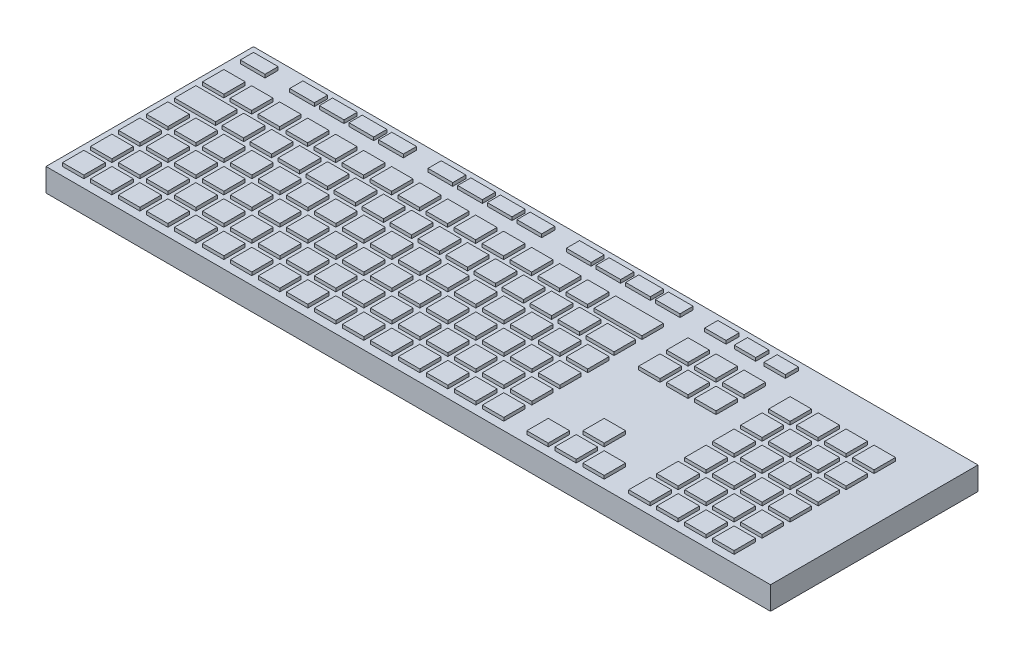
SolidWorks part; units mm, degrees
ref_plane "Front Plane" through (0, 0, 0) normal (0, 0, 1) x (1, 0, 0)
ref_plane "Top Plane" through (0, 0, 0) normal (0, 1, 0) x (1, 0, 0)
ref_plane "Right Plane" through (0, 0, 0) normal (1, 0, 0) x (0, 0, -1)
sketch "Sketch1" plane through (0, 0, 0) normal (0, 1, 0) x (1, 0, 0)
  line L1 (-220, -63) -> (220, -63)
  line L2 (-220, -63) -> (-220, 63)
  line L3 (-220, 63) -> (220, 63)
  line L4 (220, -63) -> (220, 63)
  line L5 (-220, -63) -> (220, 63) construction
  line L6 (-220, 63) -> (220, -63) construction
  point P0 (0, 0)
  dimension "D1" = 440
  dimension "D2" = 126
extrude "Boss-Extrude1" add sketch "Sketch1" along normal blind 14
sketch "Sketch4" plane through (0, 14, 0) normal (0, 1, 0) x (1, 0, 0)
  line L0 (220, 63) -> (-220, 63) construction
  line L1 (-215, 58) -> (-200, 58)
  line L2 (-215, 58) -> (-215, 50)
  line L3 (-215, 50) -> (-200, 50)
  line L4 (-200, 58) -> (-200, 50)
  line L5 (-220, 63) -> (-220, -63) construction
  dimension "D1" = 5
  dimension "D2" = 5
  dimension "D3" = 15
  dimension "D4" = 8
extrude "Boss-Extrude2" add sketch "Sketch4" along normal blind 2
sketch "Sketch5" plane through (0, 14, 0) normal (0, 1, 0) x (1, 0, 0)
  line L0 (-200, 50) -> (-200, 58) construction
  line L1 (-185, 58) -> (-170, 58)
  line L2 (-185, 58) -> (-185, 50)
  line L3 (-185, 50) -> (-170, 50)
  line L4 (-170, 58) -> (-170, 50)
  line L5 (220, 63) -> (-220, 63) construction
  point P6 (-200, 54)
  dimension "D1" = 15
  dimension "D2" = 5
  dimension "D3" = 8
  dimension "D4" = 15
extrude "Boss-Extrude3" add sketch "Sketch5" along normal blind 2
pattern_linear "LPattern1" count 4 spacing 18 along (1, 0, 0) of "Boss-Extrude3"
sketch "Sketch6" plane through (0, 14, 0) normal (0, 1, 0) x (1, 0, 0)
  line L0 (-116, 50) -> (-116, 58) construction
  line L1 (-101, 58) -> (-86, 58)
  line L2 (-101, 58) -> (-101, 50)
  line L3 (-101, 50) -> (-86, 50)
  line L4 (-86, 58) -> (-86, 50)
  line L5 (220, 63) -> (-220, 63) construction
  dimension "D1" = 15
  dimension "D2" = 5
  dimension "D3" = 8
  dimension "D4" = 15
extrude "Boss-Extrude4" add sketch "Sketch6" along normal blind 2
pattern_linear "LPattern2" count 4 spacing 18 along (1, 0, 0) of "Boss-Extrude4"
sketch "Sketch7" plane through (0, 14, 0) normal (0, 1, 0) x (1, 0, 0)
  line L0 (220, 63) -> (-220, 63) construction
  line L1 (-17, 58) -> (-2, 58)
  line L2 (-17, 58) -> (-17, 50)
  line L3 (-17, 50) -> (-2, 50)
  line L4 (-2, 58) -> (-2, 50)
  line L5 (-32, 50) -> (-32, 58) construction
  dimension "D1" = 5
  dimension "D2" = 15
  dimension "D3" = 8
  dimension "D4" = 15
extrude "Boss-Extrude5" add sketch "Sketch7" along normal blind 2
pattern_linear "LPattern3" count 4 spacing 18 along (1, 0, 0) of "Boss-Extrude5"
sketch "Sketch8" plane through (0, 14, 0) normal (0, 1, 0) x (1, 0, 0)
  line L0 (220, 63) -> (-220, 63) construction
  line L1 (67, 58) -> (80, 58)
  line L2 (67, 58) -> (67, 50)
  line L3 (67, 50) -> (80, 50)
  line L4 (80, 58) -> (80, 50)
  line L5 (52, 50) -> (52, 58) construction
  dimension "D1" = 5
  dimension "D2" = 15
  dimension "D3" = 13
  dimension "D4" = 8
extrude "Boss-Extrude6" add sketch "Sketch8" along normal blind 2
pattern_linear "LPattern4" count 3 spacing 18 along (1, 0, 0) of "Boss-Extrude6"
sketch "Sketch9" plane through (0, 14, 0) normal (0, 1, 0) x (1, 0, 0)
  line L0 (-215, 50) -> (-200, 50) construction
  line L1 (-215, 40) -> (-202, 40)
  line L2 (-215, 40) -> (-215, 27)
  line L3 (-215, 27) -> (-202, 27)
  line L4 (-202, 40) -> (-202, 27)
  line L5 (-220, 63) -> (-220, -63) construction
  dimension "D1" = 10
  dimension "D2" = 13
  dimension "D3" = 13
  dimension "D4" = 5
extrude "Boss-Extrude7" add sketch "Sketch9" along normal blind 2
sketch "Sketch10" plane through (0, 14, 0) normal (0, 1, 0) x (1, 0, 0)
  line L0 (-202, 27) -> (-202, 40) construction
  line L1 (-198, 39.8826) -> (-185, 39.8826)
  line L2 (-198, 39.8826) -> (-198, 26.8826)
  line L3 (-198, 26.8826) -> (-185, 26.8826)
  line L4 (-185, 39.8826) -> (-185, 26.8826)
  dimension "D1" = 4
  dimension "D2" = 13
  dimension "D3" = 13
extrude "Boss-Extrude8" add sketch "Sketch10" along normal blind 2
pattern_linear "LPattern5" count 13 spacing 17 along (1, 0, 0) of "Boss-Extrude8"
sketch "Sketch11" plane through (0, 14, 0) normal (0, 1, 0) x (1, 0, 0)
  line L0 (19, 39.8826) -> (6, 39.8826) construction
  line L1 (23, 39.8826) -> (52, 39.8826)
  line L2 (23, 39.8826) -> (23, 26.8826)
  line L3 (23, 26.8826) -> (52, 26.8826)
  line L4 (52, 39.8826) -> (52, 26.8826)
  line L5 (6, 26.8826) -> (19, 26.8826) construction
  line L6 (19, 26.8826) -> (19, 39.8826) construction
  line L7 (52, 50) -> (52, 58) construction
  dimension "D1" = 0
  dimension "D2" = 0
  dimension "D3" = 4
  dimension "D4" = 0
extrude "Boss-Extrude9" add sketch "Sketch11" along normal blind 2
sketch "Sketch12" plane through (0, 14, 0) normal (0, 1, 0) x (1, 0, 0)
  line L0 (-215, 40) -> (-215, 27) construction
  line L1 (-215, 23) -> (-190, 23)
  line L2 (-215, 23) -> (-215, 10)
  line L3 (-215, 10) -> (-190, 10)
  line L4 (-190, 23) -> (-190, 10)
  line L5 (-215, 27) -> (-202, 27) construction
  dimension "D1" = 0
  dimension "D2" = 13
  dimension "D3" = 4
  dimension "D4" = 25
extrude "Boss-Extrude10" add sketch "Sketch12" along normal blind 2
sketch "Sketch13" plane through (0, 14, 0) normal (0, 1, 0) x (1, 0, 0)
  line L0 (-190, 23) -> (-215, 23) construction
  line L1 (-186, 23) -> (-173, 23)
  line L2 (-186, 23) -> (-186, 10)
  line L3 (-186, 10) -> (-173, 10)
  line L4 (-173, 23) -> (-173, 10)
  line L5 (-215, 10) -> (-190, 10) construction
  line L6 (-190, 10) -> (-190, 23) construction
  dimension "D1" = 0
  dimension "D2" = 0
  dimension "D3" = 4
  dimension "D4" = 13
extrude "Boss-Extrude11" add sketch "Sketch13" along normal blind 2
pattern_linear "LPattern6" count 13 spacing 17 along (1, 0, 0) of "Boss-Extrude11"
sketch "Sketch14" plane through (0, 14, 0) normal (0, 1, 0) x (1, 0, 0)
  line L0 (31, 10) -> (31, 23) construction
  line L1 (35, 23) -> (52, 23)
  line L2 (35, 23) -> (35, 10)
  line L3 (35, 10) -> (52, 10)
  line L4 (52, 23) -> (52, 10)
  line L5 (52, 26.8826) -> (52, 39.8826) construction
  line L6 (31, 23) -> (18, 23) construction
  line L7 (18, 10) -> (31, 10) construction
  dimension "D1" = 4
  dimension "D2" = 0
  dimension "D3" = 0
  dimension "D4" = 0
extrude "Boss-Extrude12" add sketch "Sketch14" along normal blind 2
sketch "Sketch15" plane through (0, 14, 0) normal (0, 1, 0) x (1, 0, 0)
  line L0 (-215, 23) -> (-215, 10) construction
  line L1 (-215, 6) -> (-202, 6)
  line L2 (-215, 6) -> (-215, -7)
  line L3 (-215, -7) -> (-202, -7)
  line L4 (-202, 6) -> (-202, -7)
  line L5 (-215, 10) -> (-190, 10) construction
  dimension "D1" = 0
  dimension "D2" = 4
  dimension "D3" = 13
  dimension "D4" = 13
extrude "Boss-Extrude13" add sketch "Sketch15" along normal blind 2
pattern_linear "LPattern7" count 16 spacing 17 along (1, 0, 0) count 4 spacing 17 along (0, 0, 1) of "Boss-Extrude13"
sketch "Sketch16" plane through (0, 14, 0) normal (0, 1, 0) x (1, 0, 0)
  line L1 (67, 39.8826) -> (80, 39.8826)
  line L2 (67, 39.8826) -> (67, 26.8826)
  line L3 (67, 26.8826) -> (80, 26.8826)
  line L4 (80, 39.8826) -> (80, 26.8826)
  line L5 (52, 39.8826) -> (23, 39.8826) construction
  line L6 (23, 26.8826) -> (52, 26.8826) construction
  line L7 (67, 58) -> (67, 50) construction
  dimension "D1" = 0
  dimension "D2" = 0
  dimension "D3" = 0
  dimension "D4" = 13
extrude "Boss-Extrude14" add sketch "Sketch16" along normal blind 2
pattern_linear "LPattern8" count 3 spacing 17 along (1, 0, 0) count 2 spacing 17 along (0, 0, 1) of "Boss-Extrude14"
sketch "Sketch17" plane through (0, 14, 0) normal (0, 1, 0) x (1, 0, 0)
  line L0 (114, 26.8826) -> (114, 39.8826) construction
  line L1 (129, 39.8826) -> (142, 39.8826)
  line L2 (129, 39.8826) -> (129, 26.8826)
  line L3 (129, 26.8826) -> (142, 26.8826)
  line L4 (142, 39.8826) -> (142, 26.8826)
  line L5 (114, 39.8826) -> (101, 39.8826) construction
  line L6 (101, 26.8826) -> (114, 26.8826) construction
  dimension "D1" = 15
  dimension "D2" = 0
  dimension "D3" = 0
  dimension "D4" = 13
extrude "Boss-Extrude15" add sketch "Sketch17" along normal blind 2
pattern_linear "LPattern9" count 4 spacing 17 along (1, 0, 0) count 6 spacing 17 along (0, 0, 1) of "Boss-Extrude15"
sketch "Sketch18" plane through (0, 14, 0) normal (0, 1, 0) x (1, 0, 0)
  line L0 (53, -28) -> (40, -28) construction
  line L1 (84, -28) -> (97, -28)
  line L2 (84, -28) -> (84, -41)
  line L3 (84, -41) -> (97, -41)
  line L4 (97, -28) -> (97, -41)
  line L5 (40, -41) -> (53, -41) construction
  line L7 (84, 22.8826) -> (84, 9.8826) construction
  point P8 (84, -34.5)
  dimension "D1" = 0
  dimension "D2" = 0
  dimension "D3" = 13
  dimension "D4" = 0
extrude "Boss-Extrude16" add sketch "Sketch18" along normal blind 2
sketch "Sketch19" plane through (0, 14, 0) normal (0, 1, 0) x (1, 0, 0)
  line L0 (53, -45) -> (40, -45) construction
  line L1 (67, -45) -> (80, -45)
  line L2 (67, -45) -> (67, -58)
  line L3 (67, -58) -> (80, -58)
  line L4 (80, -45) -> (80, -58)
  line L5 (40, -58) -> (53, -58) construction
  line L8 (67, 22.8826) -> (67, 9.8826) construction
  line L9 (80, 9.8826) -> (80, 22.8826) construction
  dimension "D1" = 0
  dimension "D2" = 0
  dimension "D3" = 0
  dimension "D4" = 0
extrude "Boss-Extrude17" add sketch "Sketch19" along normal blind 2
pattern_linear "LPattern10" count 3 spacing 17 along (1, 0, 0) of "Boss-Extrude17"
